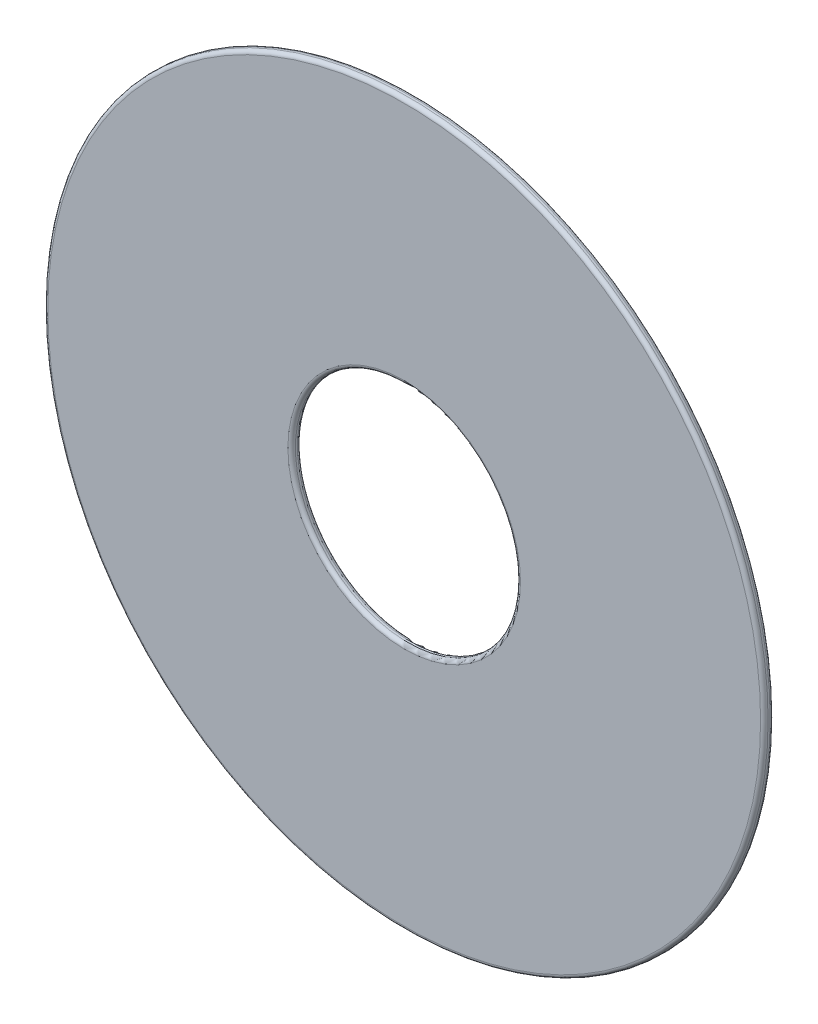
SolidWorks part; units mm, degrees
material "6061-T6 (SS)"
ref_plane "Front Plane" through (0, 0, 0) normal (0, 0, 1) x (1, 0, 0)
ref_plane "Top Plane" through (0, 0, 0) normal (0, 1, 0) x (1, 0, 0)
ref_plane "Right Plane" through (0, 0, 0) normal (1, 0, 0) x (0, 0, -1)
sketch "Sketch1" plane through (0, 0, 0) normal (0, 0, 1) x (1, 0, 0)
  circle A0 centre (0, 0) radius 24
  circle A1 centre (0, 0) radius 7.5
  dimension "D1" = 48
  dimension "D2" = 15
extrude "Boss-Extrude1" add sketch "Sketch1" along normal blind 0.64
fillet "Fillet1" radius 0.25 4 edges at (7.5, 0, 0) (7.5, 0, 0.64) (24, 0, 0) (24, 0, 0.64)
